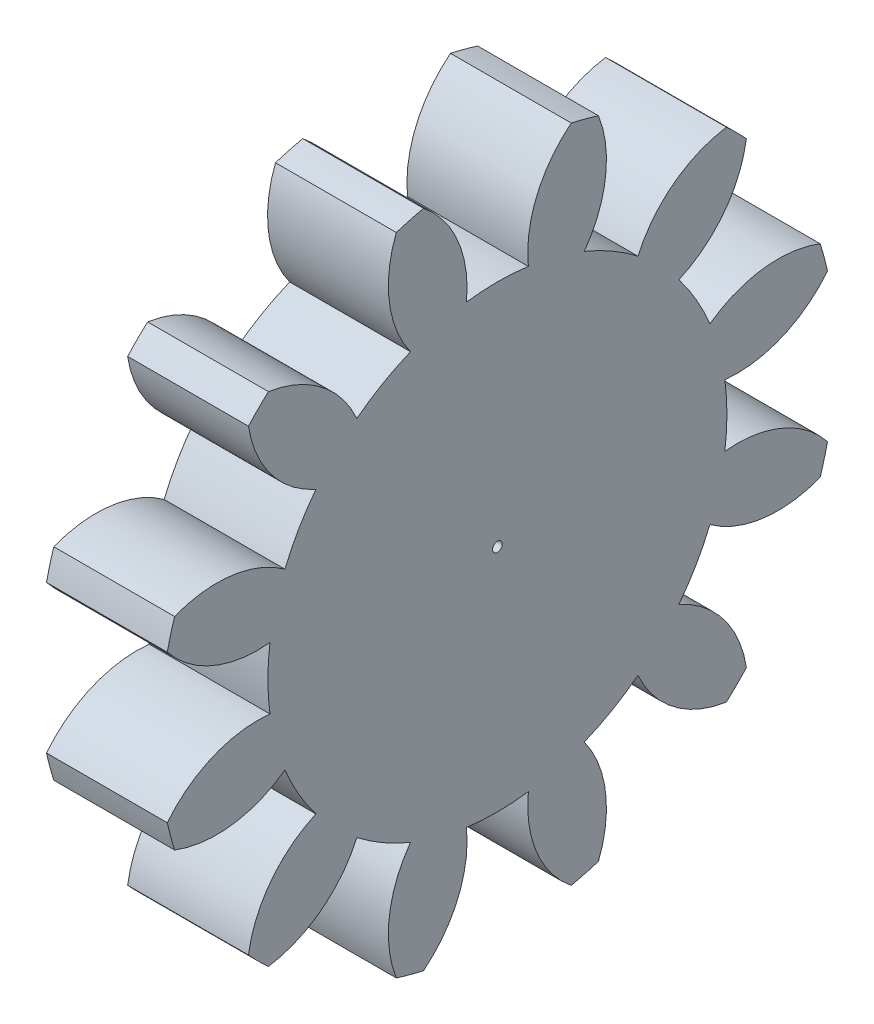
SolidWorks part; units mm, degrees
ref_plane "Plane1" through (0, 0, 0) normal (0, 0, 1) x (1, 0, 0)
ref_plane "Plane2" through (0, 0, 0) normal (0, 1, 0) x (1, 0, 0)
ref_plane "Plane3" through (0, 0, 0) normal (1, 0, 0) x (0, 0, -1)
other "Configuration Table"
sketch "HoldingSke" plane through (0, 0, 0) normal (0, 1, 0) x (1, 0, 0)
  line L0 (0, 0) -> (0.2445, -0.052)
  line L1 (-15, 0) -> (100, 0) construction
  line L2 (0, 0) -> (-2.1039, 2.3779)
  line L3 (0, 0) -> (-11.863, 4.5341)
  line L4 (0, 0) -> (8.4473, 1.7955)
  line L5 (0, 0) -> (-46.8476, -17.4728)
  line L6 (0, 0) -> (-8.2896, -5.593)
  line L7 (-2.1039, 2.3779) -> (8.6586, 51.2059)
  line L8 (-76.2, 54.61) -> (-76.1, 54.61)
  line L9 (-67.7845, 28.3722) -> (-49.3413, 33.142)
  line L10 (-76.2, 71.12) -> (104.1128, 71.12)
  line L11 (0, 0) -> (-10, 0)
  line L12 (-76.2, 101.6) -> (-76.073, 101.6)
  line L13 (24.9733, 27.94) -> (52.9518, 28.4284)
  line L14 (24.9733, 27.94) -> (24.9743, 27.94)
  line L15 (24.9733, 27.94) -> (100.4006, 29.5858)
  line L16 (-63.627, -4) -> (-12.827, -4)
  circle A0 centre (0, 0) radius 0.4
  circle A1 centre (0, 0) radius 18.999
  circle A2 centre (0, 0) radius 37.5
  circle A3 centre (0, 0) radius 0.4
  dimension "MHD" = 37.998
  dimension "Hub_dia" = 75
  dimension "Bore" = 0.8
  dimension "MBD" = 0.8
  dimension "Num_teeth" = 12
  dimension "Pitch" = 0.25
  dimension "Overall_len" = 50
  dimension "Show_teeth" = 12
  dimension "Thickness" = 10
  dimension "OAL" = 50.0001
  dimension "T_dim" = 0.1
  dimension "Ap" = 14.5
  dimension "H" = 19.05
  dimension "Pitch_radius" = 180.3128
  dimension "Width" = 10
  dimension "Backlash" = 0.127
  dimension "Addendum_fac" = 1
  dimension "Dedendum_fac" = 1.25
  dimension "Clearance_fac" = 0.25
  dimension "Dedendum_add" = 0.001
  dimension "Module" = 4
sketch "BasProSke" plane through (0, 0, 0) normal (0, 1, 0) x (1, 0, 0)
  line L0 (-10, 0) -> (60, 0) construction
  line L1 (0, 0) -> (0, 28)
  line L2 (0, 0) -> (10, 0)
  line L3 (10, 0) -> (10, 28)
  line L4 (10, 28) -> (0, 28)
  dimension "Thickness" = 10
  dimension "Diameter" = 56
revolve "Base-Revolve" add sketch "BasProSke" angle 360 about L0
sketch "TooCutSke" plane through (0, 0, 0) normal (1, 0, 0) x (0, 0, -1)
  line L1 (0, 0) -> (0, 107) construction
  line L2 (0, 0) -> (-3.3546, 23.7644) construction
  line L3 (0, 0) -> (-12.3316, 46.0223) construction
  line L4 (-3.3546, 23.7644) -> (-6.1658, 23.0111) construction
  arc A0 (2.5638, 18.8252) -> (-2.5638, 18.8252) centre (0, 0) ccw
  arc A1 (6.138, 27.345) -> (-6.138, 27.345) centre (0, 0) ccw
  circle A2 centre (0, 0) radius 24 construction
  circle A3 centre (0, 0) radius 23.2355 construction
  arc A4 (-2.5638, 18.8252) -> (-6.138, 27.345) centre (-12.1111, 19.8295) ccw
  arc A5 (6.138, 27.345) -> (2.5638, 18.8252) centre (12.1111, 19.8295) ccw
  dimension "Root_dia" = 37.998
  dimension "Overcut_dia" = 56.0508
  dimension "Pitch_dia" = 48
  dimension "Base_dia" = 46.4711
  dimension "Flank_rad" = 9.6
  dimension "Half_ang" = 15
  dimension "Half_CT" = 2.9104
extrude "ToothCut" cut sketch "TooCutSke" along normal through all
fillet "Breaks" [suppressed] radius 0.08
fillet "RootFillets" [suppressed] radius 1.001
pattern_circular "TeethCuts" count 12 every 30 about axis through (-10, 0, 0) along (1, 0, 0) of "ToothCut", "RootFillets", "Breaks"
sketch "HubNeaOneSke" plane through (0, 0, 0) normal (-1, 0, 0) x (0, 0, 1)
  circle A0 centre (0, 0) radius 18.999
  dimension "Diameter" = 37.998
extrude "HubNearOne" [suppressed] add sketch "HubNeaOneSke" along normal blind 40.0001
sketch "HubNeaBotSke" plane through (0, 0, 0) normal (-1, 0, 0) x (0, 0, 1)
  circle A0 centre (0, 0) radius 18.999
  dimension "Diameter" = 37.998
extrude "HubNearBoth" [suppressed] add sketch "HubNeaBotSke" along normal blind 20
ref_plane "FarPln" through (10, 0, 0) normal (1, 0, 0) x (0, 0, -1)
sketch "HubFarSke" plane through (10, 0, 0) normal (1, 0, 0) x (0, 0, -1)
  circle A0 centre (0, 0) radius 18.999
  dimension "Diameter" = 37.998
extrude "HubFar" [suppressed] add sketch "HubFarSke" along normal blind 20
sketch "BorSke" plane through (0, 0, 0) normal (1, 0, 0) x (0, 0, -1)
  circle A0 centre (0, 0) radius 0.4
  dimension "Diameter" = 0.8
extrude "Bore" cut sketch "BorSke" along normal mid plane 100.0001
sketch "KeySke" plane through (0, 0, 0) normal (1, 0, 0) x (0, 0, -1)
  line L0 (-0.05, 0) -> (-0.05, 0.5)
  line L1 (-0.05, 0.5) -> (0.05, 0.5)
  line L2 (0.05, 0.5) -> (0.05, 0)
  line L3 (0, 0) -> (0, 34) construction
  line L4 (-0.05, 0) -> (0.05, 0)
  dimension "Offset" = 0.5
  dimension "Width" = 0.1
extrude "Keyway" [suppressed] cut sketch "KeySke" along normal mid plane 100.0001
pattern_circular "Keyway2" [suppressed] count 2 every 90 about axis through (-10, 0, 0) along (1, 0, 0)
equation "' \"Module@HoldingSke\" = 6.35"
equation "' \"Num_teeth@HoldingSke\" = 12"
equation "' \"Ap@HoldingSke\" =  20"
equation "' \"Ap@HoldingSke\" = 20"
equation "' \"Width@HoldingSke\" = 0.5 * 25.4"
equation "' \"Hub_dia@HoldingSke\"= 1 * 25.4"
equation "' \"Hub_dia@HoldingSke\" = 1 * 25.4"
equation "' \"Overall_len@HoldingSke\" = 1.0 * 25.4"
equation "' \"Bore@HoldingSke\" = 0.75 * 25.4"
equation "' \"T_dim@HoldingSke\" = 0.1 * 25.4"
equation "' \"Width@KeySke\" = 0.25 * 25.4"
equation "' \"Show_teeth@HoldingSke\" = 13"
equation "' \"Backlash@HoldingSke\" = 0.009 * 25.4"
equation "' \"Addendum_fac@HoldingSke\" = 1.0"
equation "' \"Dedendum_fac@HoldingSke\" = 1.25"
equation "' \"Dedendum_add@HoldingSke\" = 0.00005 * 25.4"
equation "' \"Clearance_fac@HoldingSke\" = 0.25"
equation "\"Pitch@HoldingSke\" = 1 / \"Module@HoldingSke\""
equation "\"Overcut_dia@TooCutSke\" = (\"Num_teeth@HoldingSke\" + 2 * \"Addendum_fac@HoldingSke\") / \"Pitch@HoldingSke\" + 0.002 * 25.4"
equation "\"Pitch_dia@TooCutSke\" = \"Num_teeth@HoldingSke\" / \"Pitch@HoldingSke\""
equation "\"Base_dia@TooCutSke\" = \"Num_teeth@HoldingSke\" / \"Pitch@HoldingSke\" * cos((\"Ap@HoldingSke\"  * 3.14159265 / 180))"
equation "\"Root_dia@TooCutSke\" = (\"Num_teeth@HoldingSke\" + 2) / \"Pitch@HoldingSke\" - 2 * (\"Addendum_fac@HoldingSke\" + \"Dedendum_fac@HoldingSke\") / \"Pitch@HoldingSke\" - \"Dedendum_add@HoldingSke\" * 2"
equation "\"Half_ang@TooCutSke\" = 180 / \"Num_teeth@HoldingSke\""
equation "\"Half_CT@TooCutSke\" = \"Num_teeth@HoldingSke\" / \"Pitch@HoldingSke\" * sin((3.14159265 / 2 / \"Num_teeth@HoldingSke\")) / 2 - 7 * \"Backlash@HoldingSke\" / 4"
equation "\"Flank_rad@TooCutSke\" = \"Num_teeth@HoldingSke\" / \"Pitch@HoldingSke\" / 5"
equation "\"Radius@RootFillets\" = \"Clearance_fac@HoldingSke\" / \"Pitch@HoldingSke\" + \"Dedendum_add@HoldingSke\""
equation "\"Break_rad@Breaks\" = 0.02 / \"Pitch@HoldingSke\""
equation "\"Thickness@HoldingSke\" = \"Width@HoldingSke\""
equation "\"OAL@HoldingSke\" = \"Thickness@HoldingSke\""
equation "\"MHD@HoldingSke\" = (\"Num_teeth@HoldingSke\" + 2) / \"Pitch@HoldingSke\" - 2 * (\"Addendum_fac@HoldingSke\" + \"Dedendum_fac@HoldingSke\")  / \"Pitch@HoldingSke\" - \"Dedendum_add@HoldingSke\" * 2"
equation "\"MBD@HoldingSke\" = (\"Num_teeth@HoldingSke\" + 2) / \"Pitch@HoldingSke\" - 2 * (\"Addendum_fac@HoldingSke\" + \"Dedendum_fac@HoldingSke\")  / \"Pitch@HoldingSke\" - \"Dedendum_add@HoldingSke\" * 2 - 0.002 * 25.4"
equation "\"MHD@HoldingSke\" = ((sgn( \"MHD@HoldingSke\" - \"Hub_dia@HoldingSke\" )-1)*( \"MHD@HoldingSke\" - \"Hub_dia@HoldingSke\" ))/-2+ \"Hub_dia@HoldingSke\""
equation "\"MBD@HoldingSke\" = ((sgn( \"MBD@HoldingSke\" - \"Bore@HoldingSke\" )-1)*( \"MBD@HoldingSke\" - \"Bore@HoldingSke\" ))/-2+ \"Bore@HoldingSke\""
equation "\"OAL@HoldingSke\" = ((sgn( \"OAL@HoldingSke\" - \"Overall_len@HoldingSke\" )+1)*( \"OAL@HoldingSke\" - \"Overall_len@HoldingSke\" ))/2 + \"Overall_len@HoldingSke\" + 0.000002 * 25.4"
equation "\"Num_teeth@TeethCuts\" = int( \"Show_teeth@HoldingSke\" ) + 1"
equation "\"Num_teeth@TeethCuts\" = ((sgn( \"Num_teeth@TeethCuts\" - \"Num_teeth@HoldingSke\" )-1)*( \"Num_teeth@TeethCuts\" - \"Num_teeth@HoldingSke\" ))/-2+ \"Num_teeth@HoldingSke\""
equation "\"Num_teeth@TeethCuts\" = ((sgn( \"Num_teeth@TeethCuts\" - 2.0)+1)*( \"Num_teeth@TeethCuts\" - 2.0))/2 +2.0"
equation "\"Angle@TeethCuts\" = 360.0 / \"Num_teeth@HoldingSke\""
equation "\"Diameter@BasProSke\" = (\"Num_teeth@HoldingSke\" + 2 * \"Addendum_fac@HoldingSke\") / \"Pitch@HoldingSke\""
equation "\"Thickness@BasProSke\"  = \"Thickness@HoldingSke\""
equation "' \"Fillet_rad@BasProSke\" =  \"Thickness@HoldingSke\" * 0.05"
equation "' \"Fillet_rad@BasProSke\" = \"Thickness@HoldingSke\" * 0.05"
equation "\"MHD@HoldingSke\" = ((sgn( \"MHD@HoldingSke\" - \"Root_dia@TooCutSke\" )-1)*( \"MHD@HoldingSke\" - \"Root_dia@TooCutSke\" ))/-2+ \"Root_dia@TooCutSke\""
equation "\"Diameter@HubNeaOneSke\" = \"MHD@HoldingSke\""
equation "\"Length@HubNearOne\" = \"OAL@HoldingSke\" - \"Thickness@BasProSke\""
equation "\"Diameter@HubNeaBotSke\" = \"MHD@HoldingSke\""
equation "\"Length@HubNearBoth\" = ( \"OAL@HoldingSke\" - \"Thickness@BasProSke\" ) / 2.0"
equation "\"Thickness@FarPln\" = \"Thickness@BasProSke\""
equation "\"Diameter@HubFarSke\" = \"MHD@HoldingSke\""
equation "\"Length@HubFar\" = ( \"OAL@HoldingSke\" - \"Thickness@BasProSke\" ) / 2.0"
equation "\"Diameter@BorSke\" = \"MBD@HoldingSke\""
equation "\"D1@Bore\" = \"OAL@HoldingSke\" * 2.0"
equation "\"D1@Keyway\" = \"OAL@HoldingSke\" * 2.0"
equation "\"Offset@KeySke\" = \"T_dim@HoldingSke\" + \"MBD@HoldingSke\" / 2.0"
